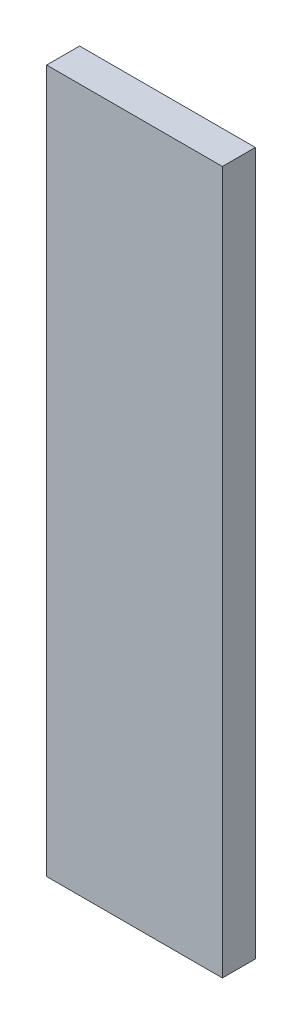
SolidWorks part; units mm, degrees
ref_plane "Front Plane" through (0, 0, 0) normal (0, 0, 1) x (1, 0, 0)
ref_plane "Top Plane" through (0, 0, 0) normal (0, 1, 0) x (1, 0, 0)
ref_plane "Right Plane" through (0, 0, 0) normal (1, 0, 0) x (0, 0, -1)
sketch "Sketch1" plane through (0, 0, 0) normal (0, 0, 1) x (1, 0, 0)
  line L1 (-12.7, -50.8) -> (12.7, -50.8)
  line L2 (-12.7, -50.8) -> (-12.7, 50.8)
  line L3 (-12.7, 50.8) -> (12.7, 50.8)
  line L4 (12.7, -50.8) -> (12.7, 50.8)
  line L5 (-12.7, -50.8) -> (12.7, 50.8) construction
  line L6 (-12.7, 50.8) -> (12.7, -50.8) construction
  point P0 (0, 0)
  dimension "D1" = 25.4
  dimension "D2" = 101.6
extrude "Boss-Extrude1" add sketch "Sketch1" along normal blind 4.7625
